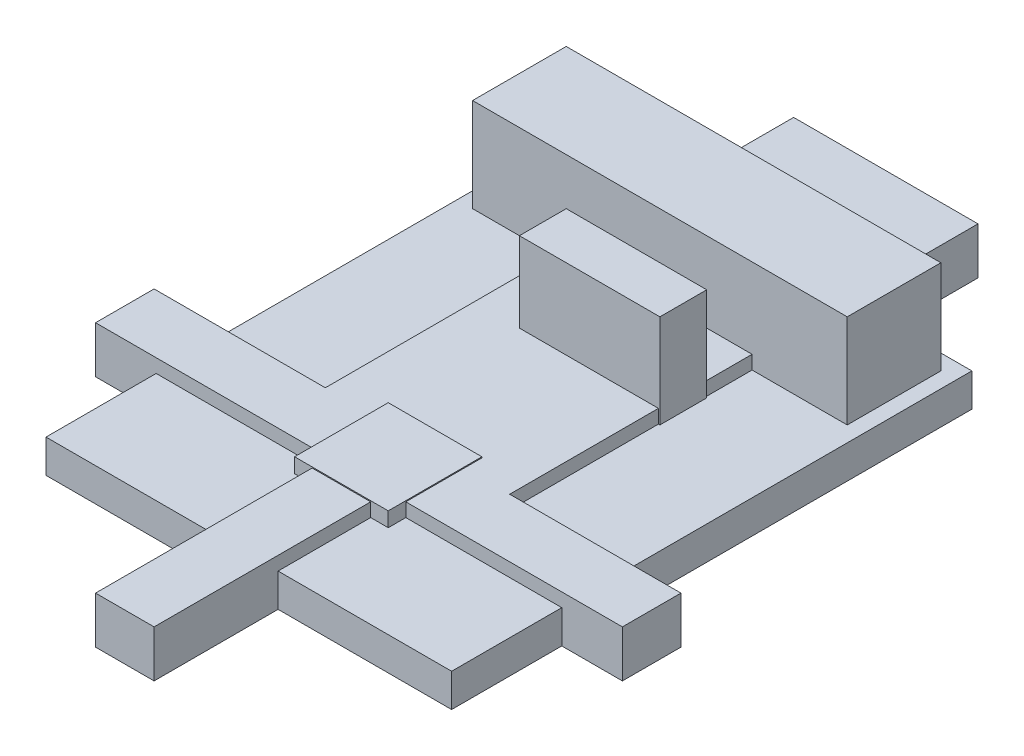
SolidWorks part; units mm, degrees
ref_plane "Front Plane" through (0, 0, 0) normal (0, 0, 1) x (1, 0, 0)
ref_plane "Top Plane" through (0, 0, 0) normal (0, 1, 0) x (1, 0, 0)
ref_plane "Right Plane" through (0, 0, 0) normal (1, 0, 0) x (0, 0, -1)
sketch "Sketch1" plane through (0, 0, 0) normal (0, 1, 0) x (1, 0, 0)
  line L9 (0, 0) -> (0, -7.5625) construction
  line L17 (-11, -7.5625) -> (11, -7.5625)
  line L18 (-11, -7.5625) -> (-11, 20.6542)
  line L19 (-11, 20.6542) -> (11, 20.6542)
  line L20 (11, -7.5625) -> (11, 20.6542)
  line L21 (-11, -7.5625) -> (11, 20.6542) construction
  line L22 (-11, 20.6542) -> (11, -7.5625) construction
  dimension "D1" = 28.2167
  dimension "D2" = 7.5625
  dimension "D6" = 22
extrude "Boss-Extrude1" add sketch "Sketch1" along normal blind 1.8
sketch "Sketch4" plane through (0, 0, 0) normal (0, 1, 0) x (1, 0, 0)
  line L0 (-14.2875, -1.5875) -> (-1.5875, -1.5875)
  line L3 (-14.2875, -1.5875) -> (14.2875, -1.5875) construction
  line L4 (-14.2875, -1.5875) -> (-14.2875, 1.5875)
  line L5 (-14.2875, 1.5875) -> (-5, 1.5875) construction
  line L6 (14.2875, -1.5875) -> (14.2875, 1.5875)
  line L7 (-14.2875, -1.5875) -> (14.2875, 1.5875) construction
  line L8 (-14.2875, 1.5875) -> (14.2875, -1.5875) construction
  line L9 (-1.5875, -14.2875) -> (1.5875, -14.2875)
  line L10 (-1.5875, -14.2875) -> (-1.5875, 26.9875) construction
  line L11 (-1.5875, 26.9875) -> (1.5875, 26.9875) construction
  line L12 (1.5875, -14.2875) -> (1.5875, 26.9875) construction
  line L13 (-1.5875, -14.2875) -> (1.5875, 26.9875) construction
  line L14 (-1.5875, 26.9875) -> (1.5875, -14.2875) construction
  line L15 (-1.5875, -1.5875) -> (-1.5875, -14.2875)
  line L16 (1.5875, -14.2875) -> (1.5875, -1.5875)
  line L17 (1.5875, -1.5875) -> (14.2875, -1.5875)
  line L18 (14.2875, 1.5875) -> (5, 1.5875)
  line L19 (1.5875, 1.5875) -> (1.5875, 26.9875) construction
  line L20 (-1.5875, 26.9875) -> (-1.5875, 1.5875) construction
  line L21 (-5, 1.5875) -> (-14.2875, 1.5875)
  line L22 (-5, 1.5875) -> (-5, 26.9875)
  line L23 (-5, 26.9875) -> (5, 26.9875)
  line L24 (5, 26.9875) -> (5, 1.5875)
  line L25 (-1.5875, 1.5875) -> (1.5875, 1.5875) construction
  line L26 (5, 1.5875) -> (14.2875, 1.5875) construction
  point P0 (0, 0)
  point P6 (0, 6.35)
  point P17 (0, 26.9875)
  point P20 (0, 26.9875)
  dimension "D1" = 12.7
  dimension "D2" = 3.175
  dimension "D3" = 10
  dimension "D4" = 25.4
extrude "Boss-Extrude4" add sketch "Sketch4" along normal blind 2.54
sketch "Sketch2" plane through (0, 1.8, 0) normal (0, 1, 0) x (1, 0, 0)
  line L10 (-2.54, -2.54) -> (2.54, -2.54)
  line L11 (-2.54, -2.54) -> (-2.54, 2.54)
  line L12 (-2.54, 2.54) -> (2.54, 2.54)
  line L13 (2.54, -2.54) -> (2.54, 2.54)
  line L14 (-2.54, -2.54) -> (2.54, 2.54) construction
  line L15 (-2.54, 2.54) -> (2.54, -2.54) construction
  point P0 (0, 0)
  dimension "D1" = 5.08
extrude "Boss-Extrude2" add sketch "Sketch2" along normal blind 0.7937
sketch "Sketch3" plane through (0, 0, 0) normal (0, -1, 0) x (-1, 0, 0)
  line L0 (-11, 20.6542) -> (-10.16, 19.8142) construction
  line L1 (-5.08, 12.1942) -> (2.54, 12.1942)
  line L2 (-5.08, 12.1942) -> (-5.08, 9.6542)
  line L3 (-5.08, 9.6542) -> (2.54, 9.6542)
  line L4 (2.54, 12.1942) -> (2.54, 9.6542)
  line L5 (-5.08, 12.1942) -> (2.54, 9.6542) construction
  line L6 (-5.08, 9.6542) -> (2.54, 12.1942) construction
  line L7 (-10.16, 19.8142) -> (10.16, 19.8142)
  line L8 (-10.16, 19.8142) -> (-10.16, 14.7342)
  line L9 (-10.16, 14.7342) -> (10.16, 14.7342)
  line L10 (10.16, 19.8142) -> (10.16, 14.7342)
  line L11 (-10.16, 19.8142) -> (10.16, 14.7342) construction
  line L12 (-10.16, 14.7342) -> (10.16, 19.8142) construction
  line L13 (10.16, 19.8142) -> (11, 20.6542) construction
  point P4 (-1.27, 10.9242)
  point P9 (0, 17.2742)
  dimension "D1" = 20.32
  dimension "D2" = 5.08
  dimension "D3" = 2.54
  dimension "D4" = 7.62
  dimension "D5" = 1.27
  dimension "D6" = 2.54
extrude "Boss-Extrude3" add sketch "Sketch3" against normal blind 5.08 from surface at -1.8 starting at face at (-5.0425, 1.8, 3.8967)
equation "\"PINWIDTH\"= .1"
equation "\"D1@Sketch3\"=\"PINWIDTH\"*8"
equation "\"D2@Sketch3\"=\"PINWIDTH\"*2"
equation "\"D3@Sketch3\"=\"PINWIDTH\""
equation "\"D4@Sketch3\"=\"PINWIDTH\"*3"
equation "\"D5@Sketch3\"=\"PINWIDTH\"*.5"
